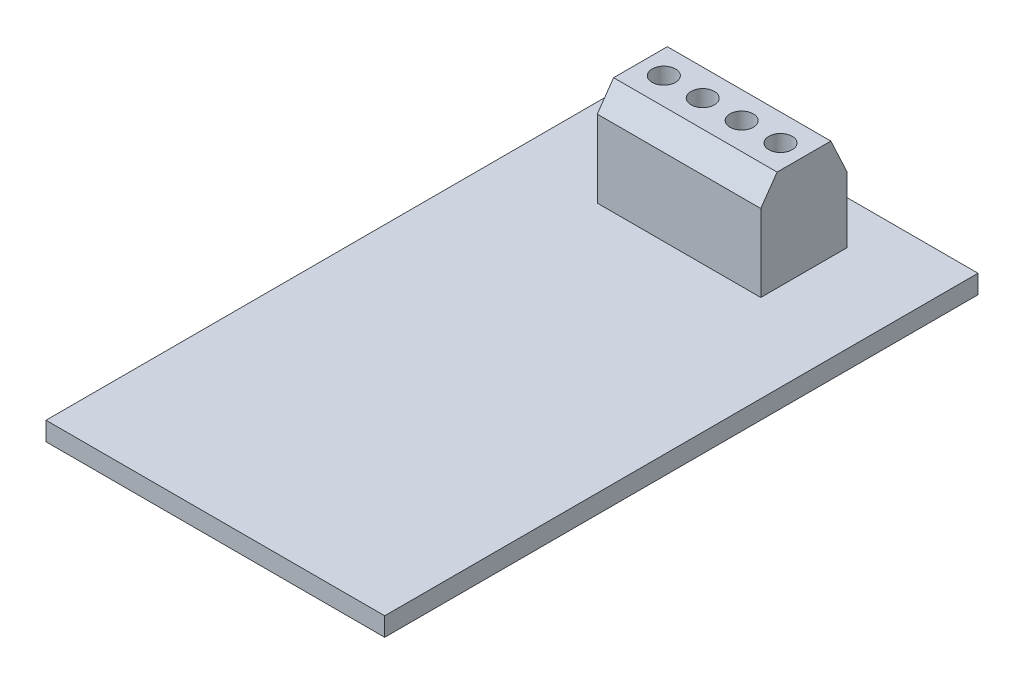
SolidWorks part; units mm, degrees
ref_plane "Alzado" through (0, 0, 0) normal (0, 0, 1) x (1, 0, 0)
ref_plane "Planta" through (0, 0, 0) normal (0, 1, 0) x (1, 0, 0)
ref_plane "Vista lateral" through (0, 0, 0) normal (1, 0, 0) x (0, 0, -1)
sketch "Croquis1" plane through (0, 0, 0) normal (0, 1, 0) x (1, 0, 0)
  line L1 (-14.5, 25.4) -> (14.5, 25.4)
  line L2 (-14.5, 25.4) -> (-14.5, -25.4)
  line L3 (-14.5, -25.4) -> (14.5, -25.4)
  line L4 (14.5, 25.4) -> (14.5, -25.4)
  line L5 (-14.5, 25.4) -> (14.5, -25.4) construction
  line L6 (-14.5, -25.4) -> (14.5, 25.4) construction
  point P0 (0, 0)
  dimension "D1" = 29
  dimension "D2" = 50.8
extrude "Saliente-Extruir1" add sketch "Croquis1" along normal blind 1.6
sketch "Croquis2" plane through (0, 0, 0) normal (1, 0, 0) x (0, 0, -1)
  line L1 (-25.4, 1.6) -> (25.4, 1.6) construction
  line L2 (14.3, 1.6) -> (14.3, 8.2)
  line L3 (14.3, 8.2) -> (15.7, 10.2)
  line L4 (15.7, 10.2) -> (20.3, 10.2)
  line L5 (20.3, 10.2) -> (21.7, 7.2)
  line L6 (21.7, 7.2) -> (21.7, 1.6)
  line L7 (21.7, 1.6) -> (14.3, 1.6)
  line L8 (25.4, 1.6) -> (25.4, 0) construction
  point P0 (21.7, 1.6)
  point P11 (25.4, 0.8)
  point P12 (0, 0)
  point P13 (18, 10.2)
  point P14 (21.7, 1.6)
  point P15 (21.7, 1.6)
  point P16 (14.3, 1.6)
  point P17 (20.3, 10.2)
  point P18 (21.7, 1.6)
  point P19 (21.7, 7.2)
  point P20 (18, 1.6)
  dimension "D1" = 3.7
  dimension "D2" = 7.4
  dimension "D3" = 8.6
  dimension "D4" = 4.6
  dimension "D5" = 5.6
  dimension "D6" = 6.6
extrude "Saliente-Extruir2" add sketch "Croquis2" along normal mid plane 14
sketch "Croquis3" plane through (0, 10.2, 0) normal (0, 1, 0) x (1, 0, 0)
  line L0 (0, 0) -> (0, 50000) construction
  line L1 (7, 20.3) -> (-7, 20.3) construction
  line L2 (-7, 18) -> (49993, 18) construction
  line L3 (-7, 20.3) -> (-7, 15.7) construction
  circle A0 centre (-5, 18) radius 1
  circle A1 centre (-1.67, 18) radius 1
  circle A2 centre (1.66, 18) radius 1
  circle A3 centre (4.99, 18) radius 1
  point P5 (0, 20.3)
  point P10 (-7, 18)
  dimension "D1" = 2
  dimension "D2" = 5
  dimension "D3" = 4
extrude "Cortar-Extruir1" cut sketch "Croquis3" against normal blind 3
